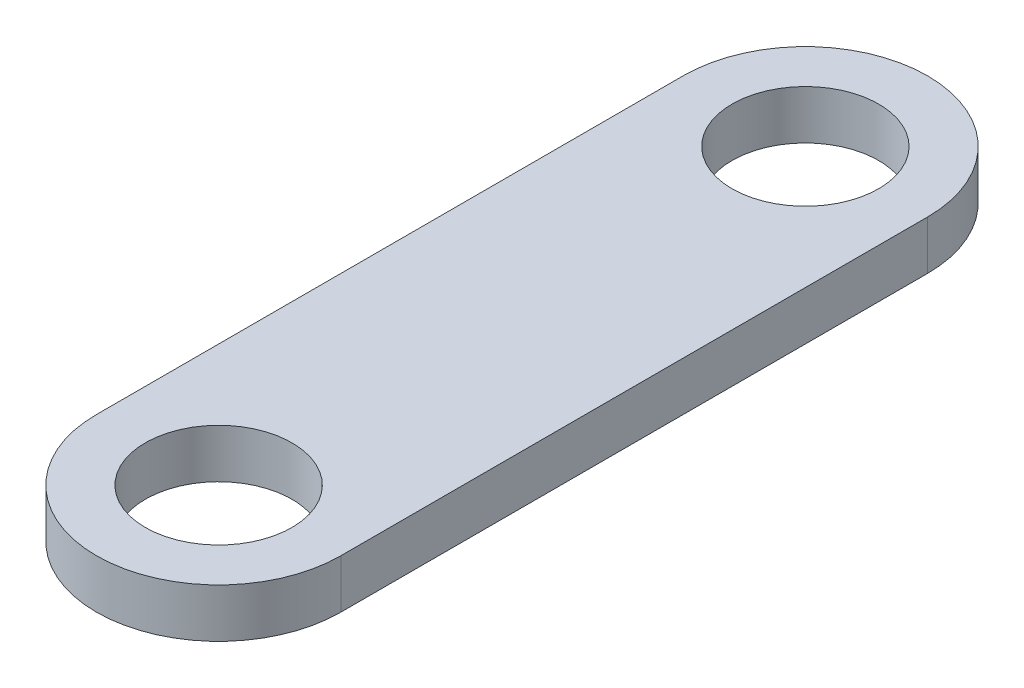
SolidWorks part; units mm, degrees
ref_plane "Front" through (0, 0, 0) normal (0, 0, 1) x (1, 0, 0)
ref_plane "Top" through (0, 0, 0) normal (0, 1, 0) x (1, 0, 0)
ref_plane "Right" through (0, 0, 0) normal (1, 0, 0) x (0, 0, -1)
sketch "草图1" plane through (0, 0, 0) normal (0, 1, 0) x (1, 0, 0)
  line L0 (-2.5, 0) -> (-2.5, -12)
  line L2 (2.5, -12) -> (2.5, 0)
  arc A0 (2.5, 0) -> (-2.5, 0) centre (0, 0) ccw
  circle A1 centre (0, 0) radius 1.5
  arc A2 (-2.5, -12) -> (2.5, -12) centre (0, -12) ccw
  circle A3 centre (0, -12) radius 1.5
extrude "凸台-拉伸1" add sketch "草图1" along normal blind 1
